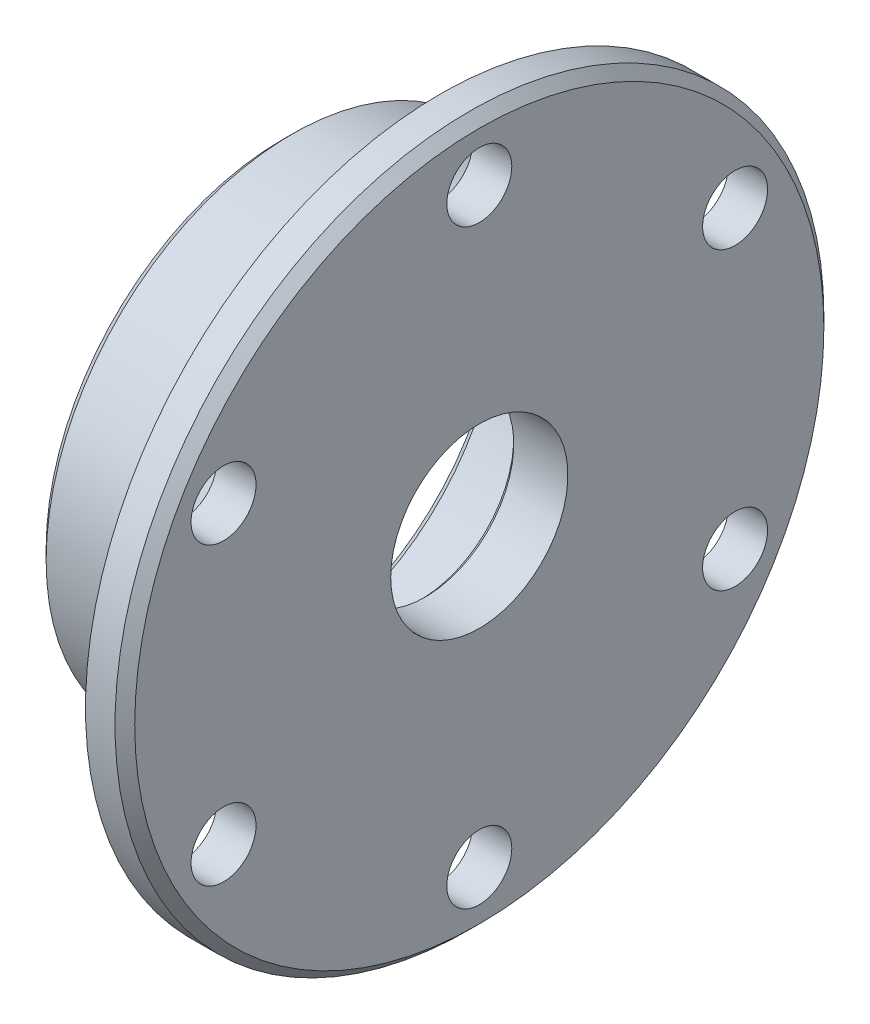
SolidWorks part; units mm, degrees
material "Сталь 20 ГОСТ 1050-88"
ref_plane "Plane1" through (0, 0, 0) normal (0, 0, 1) x (1, 0, 0)
ref_plane "Plane2" through (0, 0, 0) normal (0, 1, 0) x (1, 0, 0)
ref_plane "Plane3" through (0, 0, 0) normal (1, 0, 0) x (0, 0, -1)
sketch "Эскиз1" plane through (0, 0, 0) normal (0, 0, 1) x (1, 0, 0)
  line L0 (0, 0) -> (-30.0503, 0) construction
  line L1 (0, 36) -> (0, 0)
  line L2 (0, 36) -> (-4, 36)
  line L3 (-4, 36) -> (-4, 25)
  line L4 (-4, 25) -> (-20, 25)
  line L5 (-20, 25) -> (-20, 21)
  line L6 (-20, 21) -> (-8, 21)
  line L7 (-6, 19) -> (-6, 0)
  line L8 (-6, 0) -> (0, 0)
  line L9 (-8, 21) -> (-8, 19)
  line L10 (-8, 19) -> (-6, 19)
  dimension "D1" = 42
  dimension "D2" = 50
  dimension "D3" = 12
  dimension "D4" = 2
  dimension "D5" = 20
  dimension "D6" = 4
  dimension "D7" = 2
  dimension "D8" = 72
revolve "Повернуть1" add sketch "Эскиз1" angle 360 about L0
sketch "Эскиз2" plane through (0, 0, 0) normal (0, 0, 1) x (1, 0, 0)
  line L0 (0, 0) -> (30.4302, 0) construction
  line L1 (-20, 25) -> (-20, -25) construction
  line L2 (0, 0) -> (-20, 0)
  line L3 (0, 0) -> (0, 9)
  line L4 (0, 9) -> (-20, 9)
  line L5 (-20, 0) -> (-20, 9)
  dimension "D1" = 18
revolve "Вырез-Повернуть1" cut sketch "Эскиз2" angle 360 about L0
chamfer "Фаска1" distance 1 angle 45 2 edges at (-20, 0, -25) (-20, 0, -21)
fillet "Скругление1" radius 0.5 3 edges at (-6, 0, -19) (-8, 0, -21) (-4, 0, -25)
chamfer "Фаска2" distance 0.5 angle 45 1 edges at (-6, 0, 9)
chamfer "Фаска3" distance 1 angle 45 1 edges at (0, 0, -36)
hole_wizard "Отверстие с зазором M61" positions "Эскиз4" profile "Эскиз3" hole size "M6" standard "ISO"
sketch "Эскиз4" plane through (0, 0, 0) normal (1, 0, 0) x (0, 0, -1)
  point P0 (0, -30)
  dimension "D1" = 30
sketch "Эскиз3" plane through (0, -30, 0) normal (0, 1, 0) x (0, 0, -1)
  line L0 (0, 0) -> (0, 17.9828)
  line L1 (0, 17.9828) -> (3.3, 16)
  line L2 (3.3, 16) -> (3.3, 0)
  line L5 (3.3, 0) -> (0, 0)
  line L10 (0, 17.9828) -> (-3.3, 16) construction
  line L11 (0, -6.35) -> (0, 107.95) construction
  dimension "Диаметр отверстия" = 6.6
  dimension "Глубина отверстия" = 16
  dimension "Угол заточки сверла" = 118
pattern_circular "Круговой массив1" count 6 over 360 about axis through (0, 0, 0) along (1, 0, 0) of "Отверстие с зазором M61"
